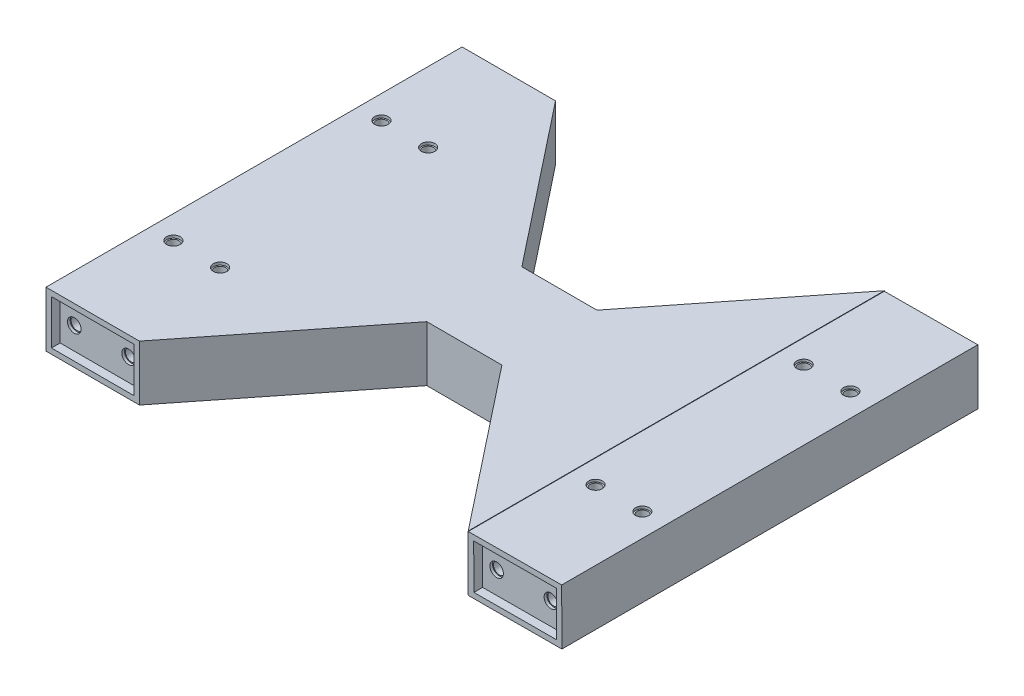
SolidWorks part; units mm, degrees
ref_plane "Front Plane" through (0, 0, 0) normal (0, 0, 1) x (1, 0, 0)
ref_plane "Top Plane" through (0, 0, 0) normal (0, 1, 0) x (1, 0, 0)
ref_plane "Right Plane" through (0, 0, 0) normal (1, 0, 0) x (0, 0, -1)
sketch "Sketch1" plane through (0, 0, 0) normal (0, 0, 1) x (1, 0, 0)
  line L12 (-28.3329, -0.106) -> (2.0671, -0.106)
  line L13 (-28.3329, 16.294) -> (-28.3329, -0.106)
  line L14 (2.0671, 16.294) -> (-28.3329, 16.294)
  line L15 (2.0671, -0.106) -> (2.0671, 16.294)
  line L16 (-30.3329, 18.294) -> (-30.3329, -2.106)
  line L17 (-30.3329, -2.106) -> (4.0671, -2.106)
  line L18 (4.0671, -2.106) -> (4.0671, 18.294)
  line L19 (4.0671, 18.294) -> (-30.3329, 18.294)
  line L24 (127.2095, -0.2643) -> (157.6092, -0.1355)
  line L25 (157.6092, -0.1355) -> (157.5398, 16.2643)
  line L26 (127.14, 16.1356) -> (127.2095, -0.2643)
  line L27 (157.5398, 16.2643) -> (127.14, 16.1356)
  line L28 (125.218, -2.2727) -> (159.6177, -2.127)
  line L29 (159.6177, -2.127) -> (159.5313, 18.2728)
  line L30 (159.5313, 18.2728) -> (125.1316, 18.1271)
  line L31 (125.1316, 18.1271) -> (125.218, -2.2727)
  dimension "D3" = 2
extrude "Boss-Extrude1" add sketch "Sketch1" along normal blind 3.2
sketch "Sketch2" plane through (0, 0, 3) normal (0, 0, 1) x (1, 0, 0)
  circle A2 centre (-23.1329, 8.094) radius 2.15
  circle A3 centre (-3.1329, 8.094) radius 2.15
  circle A6 centre (132.3747, 7.9577) radius 2.15
  circle A7 centre (152.3745, 8.0424) radius 2.15
  dimension "D1" = 4.3
  dimension "D2" = 132.3747
  dimension "D3" = 152.3745
  dimension "D4" = 3.1329
  dimension "D5" = 23.1329
  dimension "D6" = 7.9577
  dimension "D7" = 8.0424
  dimension "D8" = 8.094
sketch "Sketch4" plane through (0, 0, 3.2) normal (0, 0, 1) x (1, 0, 0)
  line L4 (4.0671, 18.294) -> (-30.3329, 18.294)
  line L5 (-30.3329, 18.294) -> (-30.3329, -2.106)
  line L6 (-30.3329, -2.106) -> (4.0671, -2.106)
  line L7 (4.0671, -2.106) -> (4.0671, 18.294)
  line L8 (4.0671, 18.294) -> (-30.3329, 18.294)
  line L9 (-30.3329, 18.294) -> (-30.3329, -2.106)
  line L10 (-30.3329, -2.106) -> (4.0671, -2.106)
  line L11 (4.0671, -2.106) -> (4.0671, 18.294)
  line L12 (125.1316, 18.1271) -> (125.218, -2.2727)
  line L13 (125.218, -2.2727) -> (159.6177, -2.127)
  line L14 (159.6177, -2.127) -> (159.5313, 18.2728)
  line L15 (159.5313, 18.2728) -> (125.1316, 18.1271)
  line L16 (125.1316, 18.1271) -> (125.218, -2.2727)
  line L17 (125.218, -2.2727) -> (159.6177, -2.127)
  line L18 (159.6177, -2.127) -> (159.5313, 18.2728)
  line L19 (159.5313, 18.2728) -> (125.1316, 18.1271)
  dimension "D1" = 0
  dimension "D2" = 0
extrude "Boss-Extrude2" add sketch "Sketch4" along normal blind 150
sketch "Sketch5" plane through (0, 0, 153.2) normal (0, 0, 1) x (1, 0, 0)
  line L8 (2.0671, -0.106) -> (2.0671, 16.294)
  line L9 (2.0671, 16.294) -> (-28.3329, 16.294)
  line L10 (-28.3329, 16.294) -> (-28.3329, -0.106)
  line L11 (-28.3329, -0.106) -> (2.0671, -0.106)
  line L12 (2.0671, -0.106) -> (2.0671, 16.294)
  line L13 (2.0671, 16.294) -> (-28.3329, 16.294)
  line L14 (-28.3329, 16.294) -> (-28.3329, -0.106)
  line L15 (-28.3329, -0.106) -> (2.0671, -0.106)
  line L20 (157.5398, 16.2643) -> (127.14, 16.1356)
  line L21 (127.14, 16.1356) -> (127.2095, -0.2643)
  line L22 (127.2095, -0.2643) -> (157.6092, -0.1355)
  line L23 (157.6092, -0.1355) -> (157.5398, 16.2643)
  line L24 (157.5398, 16.2643) -> (127.14, 16.1356)
  line L25 (127.14, 16.1356) -> (127.2095, -0.2643)
  line L26 (127.2095, -0.2643) -> (157.6092, -0.1355)
  line L27 (157.6092, -0.1355) -> (157.5398, 16.2643)
  dimension "D3" = 30.4
  dimension "D4" = 16.4
  dimension "D1" = 2
  dimension "D2" = 2
extrude "Cut-Extrude2" cut sketch "Sketch5" against normal blind 3.2
sketch "Sketch12" plane through (0, 18.294, 0) normal (0, 1, 0) x (1, 0, 0)
  line L0 (4.0671, -153.2) -> (125.0967, -153.2) construction
  point P3 (64.5819, -153.2)
sketch "Sketch13" plane through (4.0671, 0, 0) normal (1, 0, 0) x (0, 0, -1)
  line L4 (0, -2.106) -> (0, 18.294)
  line L5 (0, 18.294) -> (-153.2, 18.294)
  line L6 (-153.2, 18.294) -> (-153.2, -2.106)
  line L7 (-153.2, -2.106) -> (0, -2.106)
  line L8 (0, -2.106) -> (0, 18.294)
  line L9 (0, 18.294) -> (-153.2, 18.294)
  line L10 (-153.2, 18.294) -> (-153.2, -2.106)
  line L11 (-153.2, -2.106) -> (0, -2.106)
  dimension "D1" = 0
extrude "Boss-Extrude4" add sketch "Sketch13" along normal up to surface (121.0637 mm away)
extrude "Cut-Extrude5" cut sketch "Sketch2" along normal up to surface (147 mm away) up to face at (142.3746, 8, 150)
sketch "Sketch18" plane through (0, 0, 3.2) normal (0, 0, -1) x (-1, 0, 0)
  circle A0 centre (-132.3747, 7.9577) radius 2.5
  circle A1 centre (-152.3745, 8.0424) radius 2.5
  circle A2 centre (3.1329, 8.094) radius 2.5
  circle A3 centre (23.1329, 8.094) radius 2.5
  point P6 (-152.3745, 8.0424)
  point P9 (-132.3747, 7.9577)
  point P11 (3.1329, 8.094)
  point P13 (23.1329, 8.094)
  dimension "D1" = 5
extrude "Cut-Extrude6" cut sketch "Sketch18" against normal blind 1
sketch "Sketch19" plane through (0, 0, 150) normal (0, 0, 1) x (1, 0, 0)
  circle A0 centre (-23.1329, 8.094) radius 2.5
  circle A1 centre (-3.1329, 8.094) radius 2.5
  circle A2 centre (132.3747, 7.9577) radius 2.5
  circle A3 centre (152.3745, 8.0424) radius 2.5
  dimension "D1" = 5
extrude "Cut-Extrude7" cut sketch "Sketch19" against normal blind 1
sketch "Sketch20" plane through (-0.0745, 17.5967, 0) normal (-0.0042, 1, 0) x (1, 0.0042, 0)
  line L0 (159.6072, -153.2) -> (125.2072, -153.2) construction
  line L1 (159.6072, 0) -> (125.2072, 0) construction
  line L2 (159.6072, -153.2) -> (159.6072, 0) construction
  line L3 (125.2072, -153.2) -> (125.2072, 0) construction
  line L4 (142.4072, -153.2) -> (142.4072, -76.6) construction
  line L5 (142.4072, -76.6) -> (125.2072, -76.6) construction
  line L6 (142.4072, -76.6) -> (159.6072, -76.6) construction
  line L7 (142.4072, -76.6) -> (142.4072, 0) construction
  line L8 (125.2072, 0) -> (125.2072, -153.2) construction
  point P0 (142.4072, -153.2)
  point P1 (142.4072, 0)
  point P4 (159.6072, -76.6)
  point P7 (125.2072, -76.6)
  point P14 (142.4072, -114.9)
  point P18 (142.4072, -38.3)
  point P19 (133.8072, -76.6)
  point P20 (151.0072, -76.6)
  point P21 (151.0072, -114.9)
  point P22 (133.8072, -114.9)
  point P23 (151.0072, -38.3)
  point P24 (133.8072, -38.3)
  dimension "D1" = 8.6
  dimension "D2" = 8.6
  dimension "D3" = 38.3
hole_wizard "Ø4.0 (4) Diameter Hole1" positions "3DSketch1" profile "Sketch21" hole size "Ø4.0" standard "ANSI Metric"
sketch3d "3DSketch1"
  point P0 (133.7315, 18.1635, 114.9)
  point P3 (150.9313, 18.2364, 114.9)
  point P6 (133.7315, 18.1635, 38.3)
  point P9 (150.9313, 18.2364, 38.3)
sketch "Sketch21" plane through (133.7315, 18.1635, 114.9) normal (0, 0, 1) x (-1, -0.0042, 0)
  line L0 (0, 0) -> (0, 21.6007)
  line L1 (0, 21.6007) -> (2, 20.399)
  line L2 (2, 20.399) -> (2, 0)
  line L5 (2, 0) -> (0, 0)
  line L10 (0, 21.6007) -> (-2, 20.399) construction
  line L11 (0, -6.35) -> (0, 107.95) construction
  dimension "Hole Dia." = 4
  dimension "Hole Depth" = 20.399
  dimension "Drill Angle" = 118
sketch "Sketch22" plane through (329.1302, 18.294, 0) normal (0, -1, 0) x (-1, 0, 0)
  circle A0 centre (195.3987, -114.9) radius 2.5
  circle A1 centre (178.1989, -114.9) radius 2.5
  circle A2 centre (178.1989, -38.3) radius 2.5
  circle A3 centre (195.3987, -38.3) radius 2.5
extrude "Cut-Extrude10" cut sketch "Sketch22" along normal blind 1
sketch "Sketch26" plane through (0, 18.294, 0) normal (0, 1, 0) x (1, 0, 0)
  line L0 (4.0671, -153.2) -> (4.0671, 0)
  line L1 (125.1309, 0) -> (-30.3329, 0) construction
  line L2 (-30.3329, -153.2) -> (-30.3329, 0) construction
  line L3 (-30.3329, -76.6) -> (4.0671, -76.6) construction
  line L4 (-13.1329, -153.2) -> (-13.1329, -76.6) construction
  line L5 (125.1309, -153.2) -> (-30.3329, -153.2) construction
  line L6 (-13.1329, -76.6) -> (-13.1329, 0) construction
  line L7 (-13.1329, -38.3) -> (-30.3329, -38.3) construction
  line L8 (-13.1329, -38.3) -> (4.0671, -38.3) construction
  line L9 (-13.1329, -153.2) -> (4.0671, -153.2) construction
  point P7 (-30.3329, -76.6)
  point P8 (4.0671, -76.6)
  point P11 (-4.5329, -114.9)
  point P16 (-4.5329, -153.2)
  point P18 (-21.7329, -38.3)
  point P21 (-21.7329, -38.3)
  point P23 (-4.5329, -38.3)
  point P24 (-21.7329, -114.9)
hole_wizard "Ø4.0 (4) Diameter Hole2" positions "3DSketch2" profile "Sketch27" hole size "Ø4.0" standard "ANSI Metric"
sketch3d "3DSketch2"
  point P0 (-21.7329, 18.294, 114.9)
  point P3 (-4.5329, 18.294, 114.9)
  point P6 (-4.5329, 18.294, 38.3)
  point P9 (-21.7329, 18.294, 38.3)
sketch "Sketch27" plane through (-21.7329, 18.294, 114.9) normal (1, 0, 0) x (0, 0, 1)
  line L0 (0, 0) -> (0, 21.6007)
  line L1 (0, 21.6007) -> (2, 20.399)
  line L2 (2, 20.399) -> (2, 0)
  line L5 (2, 0) -> (0, 0)
  line L10 (0, 21.6007) -> (-2, 20.399) construction
  line L11 (0, -6.35) -> (0, 107.95) construction
  dimension "Hole Dia." = 4
  dimension "Hole Depth" = 20.399
  dimension "Drill Angle" = 118
sketch "Sketch28" plane through (0, 18.294, 0) normal (0, 1, 0) x (1, 0, 0)
  circle A0 centre (-21.7329, -38.3) radius 2.5
  circle A1 centre (-4.5329, -38.3) radius 2.5
  circle A2 centre (-21.7329, -114.9) radius 2.5
  circle A3 centre (-4.5329, -114.9) radius 2.5
extrude "Cut-Extrude11" cut sketch "Sketch28" against normal blind 1
sketch "Sketch29" plane through (0, 18.294, 0) normal (0, 1, 0) x (1, 0, 0)
  line L0 (4.0671, 0) -> (125.1309, -153.2)
  line L1 (125.1309, 0) -> (4.0671, -153.2)
  line L3 (47.099, -94.1) -> (82.099, -94.1)
  line L4 (47.099, -94.1) -> (47.099, -59.1)
  line L5 (47.099, -59.1) -> (82.099, -59.1)
  line L6 (82.099, -94.1) -> (82.099, -59.1)
  line L7 (47.099, -94.1) -> (82.099, -59.1) construction
  line L8 (47.099, -59.1) -> (82.099, -94.1) construction
  point P8 (64.599, -76.6)
  line M5 (125.1309, 0) -> (-30.3329, 0)
  line M7 (-30.3329, -153.2) -> (125.1309, -153.2)
extrude "Cut-Extrude12" cut sketch "Sketch29" against normal through all contours L3 L1 L0 M7 | L0 L5 L1 M5
